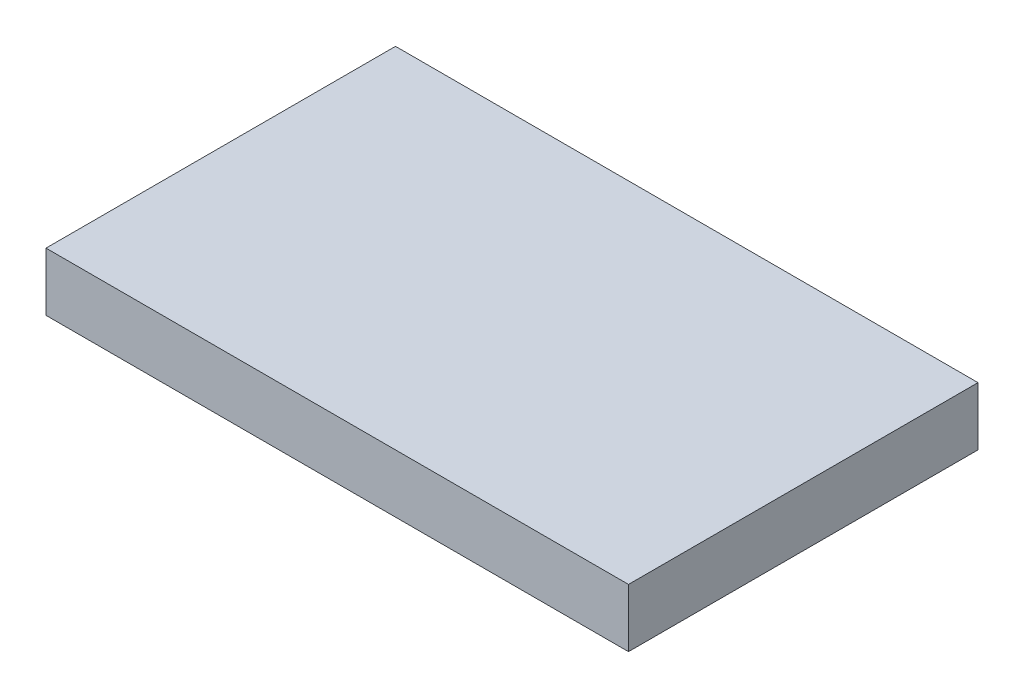
SolidWorks part; units mm, degrees
ref_plane "Front Plane" through (0, 0, 0) normal (0, 0, 1) x (1, 0, 0)
ref_plane "Top Plane" through (0, 0, 0) normal (0, 1, 0) x (1, 0, 0)
ref_plane "Right Plane" through (0, 0, 0) normal (1, 0, 0) x (0, 0, -1)
sketch "Sketch1" plane through (0, 0, 0) normal (0, 1, 0) x (1, 0, 0)
  line L1 (0, 0) -> (127, 0)
  line L2 (0, 0) -> (0, -76.2)
  line L3 (0, -76.2) -> (127, -76.2)
  line L4 (127, 0) -> (127, -76.2)
  dimension "D1" = 127
  dimension "D2" = 76.2
extrude "Boss-Extrude1" add sketch "Sketch1" along normal blind 12.7
